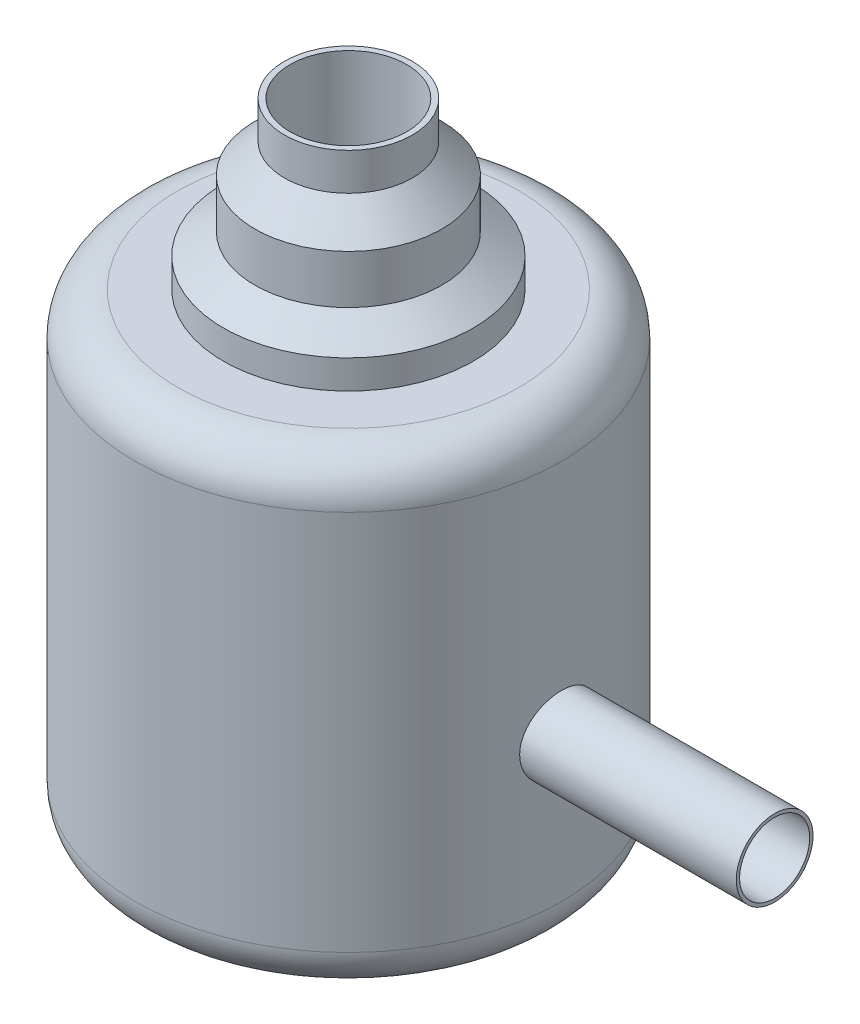
SolidWorks part; units mm, degrees
ref_plane "Front Plane" through (0, 0, 0) normal (0, 0, 1) x (1, 0, 0)
ref_plane "Top Plane" through (0, 0, 0) normal (0, 1, 0) x (1, 0, 0)
ref_plane "Right Plane" through (0, 0, 0) normal (1, 0, 0) x (0, 0, -1)
sketch "Sketch2" plane through (0, 0, 0) normal (0, 1, 0) x (1, 0, 0)
  circle A0 centre (0, 0) radius 2.5
  dimension "D1" = 5
extrude "Boss-Extrude1" add sketch "Sketch2" along normal blind 5
sketch "Sketch3" plane through (0, 0, 0) normal (0, 0, 1) x (1, 0, 0)
  line L0 (0, 0) -> (0, 7.4117) construction
  line L1 (0, 7.4117) -> (-0.75, 7.4117)
  line L2 (-2.5, 5) -> (0, 5)
  line L3 (2.5, 5) -> (-2.5, 5) construction
  line L4 (0, 5) -> (0, 7.4117)
  line L5 (-0.75, 7.4117) -> (-0.75, 6.9751)
  line L6 (-0.75, 6.9751) -> (-1.0959, 6.6292)
  line L7 (-1.0959, 6.6292) -> (-1.0959, 6.0584)
  line L8 (-1.0959, 6.0584) -> (-1.4659, 5.8092)
  line L9 (-1.4659, 5.8092) -> (-1.4659, 5.4715)
  line L10 (-1.4659, 5.4715) -> (-2.5, 5.4715)
  line L11 (-2.5, 5.4715) -> (-2.5, 5)
  dimension "D1" = 0.75
revolve "Revolve2" add sketch "Sketch3" angle 360 about L0
sketch "Sketch4" plane through (0, 7.4117, 0) normal (0, 1, 0) x (1, 0, 0)
  circle A0 centre (0, 0) radius 0.6841
extrude "Cut-Extrude1" cut sketch "Sketch4" against normal blind 5
fillet "Fillet2" radius 0.5 2 edges at (0, 0, 2.5) (0, 5.4715, -2.5)
sketch "Sketch5" plane through (0, 0, 0) normal (1, 0, 0) x (0, 0, -1)
  circle A0 centre (0, 2.1947) radius 0.45
  dimension "D1" = 0.9
extrude "Boss-Extrude2" add sketch "Sketch5" along normal blind 5
sketch "Sketch6" plane through (5, 0, 0) normal (1, 0, 0) x (0, 0, -1)
  circle A0 centre (0, 2.1947) radius 0.411
extrude "Cut-Extrude2" cut sketch "Sketch6" against normal blind 4
